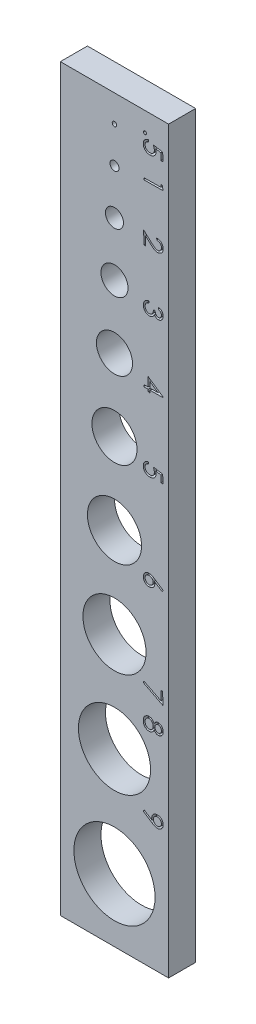
SolidWorks part; units mm, degrees
ref_plane "Front Plane" through (0, 0, 0) normal (0, 0, 1) x (1, 0, 0)
ref_plane "Top Plane" through (0, 0, 0) normal (0, 1, 0) x (1, 0, 0)
ref_plane "Right Plane" through (0, 0, 0) normal (1, 0, 0) x (0, 0, -1)
sketch "Sketch1" plane through (0, 0, 0) normal (0, 0, 1) x (1, 0, 0)
  line L0 (0, 0) -> (0, 82.2973) construction
  line L6 (-6, 75) -> (6, 75)
  line L7 (-6, 75) -> (-6, -7)
  line L8 (-6, -7) -> (6, -7)
  line L9 (6, 75) -> (6, -7)
  circle A8 centre (0, 0) radius 4.5
  circle A9 centre (0, 12) radius 4
  circle A10 centre (0, 23) radius 3.5
  circle A11 centre (0, 33) radius 3
  circle A12 centre (0, 63) radius 1
  circle A13 centre (0, 57) radius 1.5
  circle A14 centre (0, 50) radius 2
  circle A15 centre (0, 42) radius 2.5
  circle A16 centre (0, 68) radius 0.5
  circle A17 centre (0, 72) radius 0.25
  point P22 (0, 34.0663)
  dimension "D1" = 9
  dimension "D2" = 8
  dimension "D3" = 7
  dimension "D4" = 6
  dimension "D5" = 5
  dimension "D6" = 4
  dimension "D7" = 3
  dimension "D8" = 2
  dimension "D9" = 1
  dimension "D10" = 0.5
  dimension "D11" = 12
  dimension "D12" = 11
  dimension "D13" = 10
  dimension "D14" = 9
  dimension "D15" = 8
  dimension "D16" = 7
  dimension "D17" = 6
  dimension "D18" = 5
  dimension "D19" = 4
  dimension "D22" = 6
  dimension "D20" = 82
  dimension "D21" = 12
  dimension "D23" = 3
extrude "Boss-Extrude1" add sketch "Sketch1" along normal blind 3
sketch "Sketch3" plane through (0, 0, 3) normal (0, 0, 1) x (1, 0, 0)
  line L0 (3.2403, 73.3045) -> (3.2403, 5.3547) construction
  text T0 ".5  1     2      3       4        5           6           7  8         9 " font "Century Gothic" height in points 8
  point P2 (4.6304, 3.7376)
  point P3 (3.8906, 72.2815)
  point P4 (3.5229, 72.2064)
  point P5 (4.6304, 72)
  point P6 (4.6304, 6.3888)
  point P7 (4.6304, 5.645)
  point P9 (2.817, 72.6101)
  point P10 (2.0946, 72.6101)
  point P11 (3.0578, 72.5757)
  point P12 (2.5418, 72.6101)
  point P13 (2.973, 5.0004)
  point P14 (2.9327, 5.6048)
  point P15 (2.9327, 72.6794)
  point P16 (0, 0)
  point P17 (2.9327, 73.3939)
  point P18 (3.2018, 73.2275)
  point P19 (3.2403, 73.3045)
  point P20 (3.2403, 5.3547)
extrude "Cut-Extrude1" cut sketch "Sketch3" against normal blind 0.6
